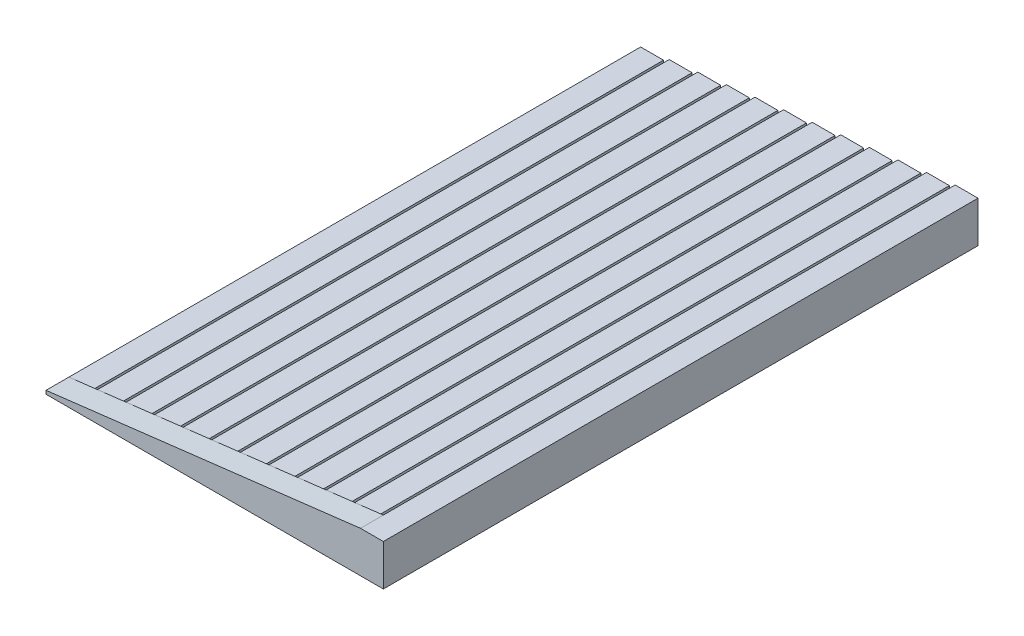
SolidWorks part; units mm, degrees
ref_plane "Front Plane" through (0, 0, 0) normal (0, 0, 1) x (1, 0, 0)
ref_plane "Top Plane" through (0, 0, 0) normal (0, 1, 0) x (1, 0, 0)
ref_plane "Right Plane" through (0, 0, 0) normal (1, 0, 0) x (0, 0, -1)
sketch "Sketch1" plane through (0, 0, 0) normal (0, 0, 1) x (1, 0, 0)
  line L0 (0, 0) -> (29.5, 0) construction
  line L2 (0, 0) -> (2, 0)
  line L3 (0, 0) -> (0, 0.3)
  line L4 (0, 0.3) -> (2, 0.3)
  line L5 (2, 0) -> (2, 0.3)
  line L6 (2.5, 0) -> (4.5, 0)
  line L7 (2.5, 0) -> (2.5, 0.6)
  line L8 (2.5, 0.6) -> (4.5, 0.6)
  line L9 (4.5, 0) -> (4.5, 0.6)
  line L10 (5, 0) -> (7, 0)
  line L11 (5, 0) -> (5, 0.9)
  line L12 (5, 0.9) -> (7, 0.9)
  line L13 (7, 0) -> (7, 0.9)
  line L14 (7.5, 0) -> (9.5, 0)
  line L15 (7.5, 0) -> (7.5, 1.2)
  line L16 (7.5, 1.2) -> (9.5, 1.2)
  line L17 (9.5, 0) -> (9.5, 1.2)
  line L18 (10, 0) -> (12, 0)
  line L19 (10, 0) -> (10, 1.5)
  line L20 (10, 1.5) -> (12, 1.5)
  line L21 (12, 0) -> (12, 1.5)
  line L22 (12.5, 0) -> (14.5, 0)
  line L23 (12.5, 0) -> (12.5, 1.8)
  line L24 (12.5, 1.8) -> (14.5, 1.8)
  line L25 (14.5, 0) -> (14.5, 1.8)
  line L26 (15, 0) -> (17, 0)
  line L27 (15, 0) -> (15, 2.1)
  line L28 (15, 2.1) -> (17, 2.1)
  line L29 (17, 0) -> (17, 2.1)
  line L30 (17.5, 0) -> (19.5, 0)
  line L31 (17.5, 0) -> (17.5, 2.4)
  line L32 (17.5, 2.4) -> (19.5, 2.4)
  line L33 (19.5, 0) -> (19.5, 2.4)
  line L34 (20, 0) -> (22, 0)
  line L35 (20, 0) -> (20, 2.7)
  line L36 (20, 2.7) -> (22, 2.7)
  line L37 (22, 0) -> (22, 2.7)
  line L38 (22.5, 0) -> (24.5, 0)
  line L39 (22.5, 0) -> (22.5, 3)
  line L40 (22.5, 3) -> (24.5, 3)
  line L41 (24.5, 0) -> (24.5, 3)
  line L42 (25, 0) -> (27, 0)
  line L43 (25, 0) -> (25, 3.3)
  line L44 (25, 3.3) -> (27, 3.3)
  line L45 (27, 0) -> (27, 3.3)
  line L46 (27.5, 0) -> (29.5, 0)
  line L47 (27.5, 0) -> (27.5, 3.6)
  line L48 (27.5, 3.6) -> (29.5, 3.6)
  line L49 (29.5, 0) -> (29.5, 3.6)
  point P23 (0, 0.15)
  point P51 (29.804, 0)
  dimension "D1" = 0.3
  dimension "D2" = 0.6
  dimension "D3" = 0.9
  dimension "D4" = 1.2
  dimension "D5" = 1.5
  dimension "D6" = 2
  dimension "D7" = 2
  dimension "D8" = 2
  dimension "D9" = 2
  dimension "D10" = 2
  dimension "D11" = 0.5
  dimension "D12" = 0.5
  dimension "D13" = 0.5
  dimension "D14" = 0.5
  dimension "D15" = 2
  dimension "D16" = 2
  dimension "D17" = 2
  dimension "D18" = 2
  dimension "D19" = 2
  dimension "D20" = 2
  dimension "D21" = 2
  dimension "D22" = 1.8
  dimension "D23" = 2.1
  dimension "D24" = 2.4
  dimension "D25" = 2.7
  dimension "D26" = 3
  dimension "D27" = 3.3
  dimension "D28" = 3.6
  dimension "D29" = 0.5
  dimension "D30" = 0.5
  dimension "D31" = 0.5
  dimension "D32" = 0.5
  dimension "D33" = 0.5
  dimension "D34" = 0.5
  dimension "D35" = 0.5
extrude "Boss-Extrude1" add sketch "Sketch1" along normal blind 50
sketch "Sketch2" plane through (0, 0, 50) normal (0, 0, 1) x (1, 0, 0)
  line L0 (0, 0) -> (29.5, 0)
  line L1 (29.5, 0) -> (29.5, 3.6)
  line L2 (29.5, 3.6) -> (27.5, 3.6)
  line L3 (27.5, 3.6) -> (0, 0.3)
  line L4 (0, 0.3) -> (0, 0)
extrude "Boss-Extrude2" add sketch "Sketch2" along normal blind 2
